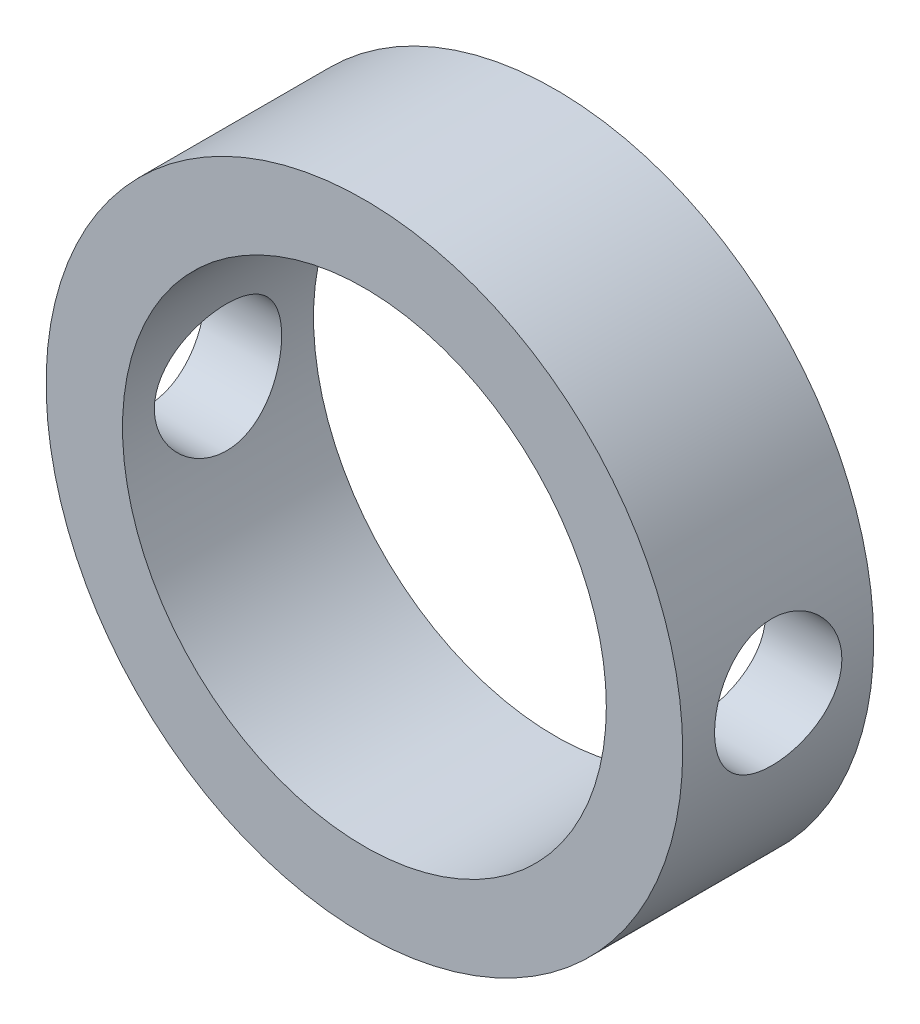
SolidWorks part; units mm, degrees
material "Gerais  - 6061-T6"
ref_plane "Plano frontal" through (0, 0, 0) normal (0, 0, 1) x (1, 0, 0)
ref_plane "Plano superior" through (0, 0, 0) normal (0, 1, 0) x (1, 0, 0)
ref_plane "Plano direito" through (0, 0, 0) normal (1, 0, 0) x (0, 0, -1)
sketch "Esboço1" plane through (0, 0, 0) normal (0, 0, 1) x (1, 0, 0)
  circle A0 centre (0, 0) radius 10
  circle A1 centre (0, 0) radius 7.6
  dimension "D1" = 20
  dimension "D2" = 15.2
extrude "Ressalto-extrusão1" add sketch "Esboço1" along normal blind 6
sketch "Esboço2" plane through (0, 0, 0) normal (1, 0, 0) x (0, 0, -1)
  line L0 (0, 10) -> (-6, 10) construction
  circle A0 centre (-3, 0) radius 2
  point P2 (-3, 10)
  dimension "D1" = 4
extrude "Corte-extrusão1" cut sketch "Esboço2" against normal through all both and the other way through all
